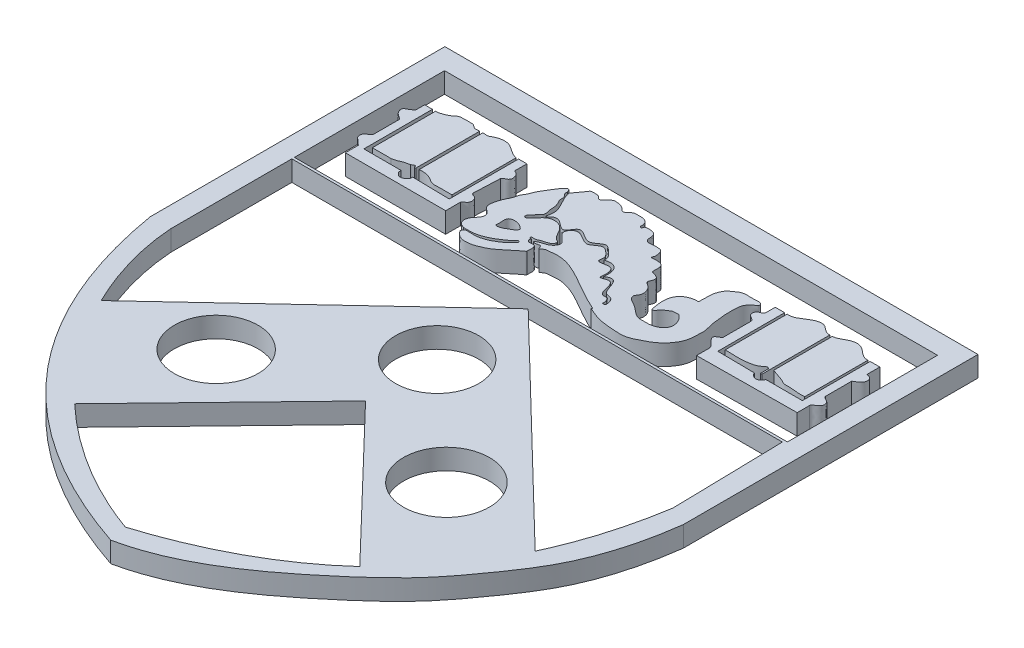
SolidWorks part; units mm, degrees
ref_plane "Front Plane" through (0, 0, 0) normal (0, 0, 1) x (1, 0, 0)
ref_plane "Top Plane" through (0, 0, 0) normal (0, 1, 0) x (1, 0, 0)
ref_plane "Right Plane" through (0, 0, 0) normal (1, 0, 0) x (0, 0, -1)
sketch "Sketch1" plane through (0, 0, 0) normal (0, 1, 0) x (1, 0, 0)
  line L0 (1055.163, 2168.8865) -> (3721.8297, 2168.8865) construction
  line L1 (1053.545, 3653.5487) -> (1053.545, 3267.9613)
  line L2 (1297.9682, 3681.7333) -> (1297.9682, 3287.744)
  line L3 (1316.3208, 3681.7333) -> (1316.3208, 3287.744)
  line L4 (1554.0703, 3653.5487) -> (1554.0703, 3254.3888)
  line L5 (1568.2519, 3653.5487) -> (1568.2519, 3223.5903)
  line L6 (1568.2519, 3653.5487) -> (1619.9728, 3653.5487)
  line L7 (1619.9728, 3653.5487) -> (1619.9728, 3576.7685)
  line L8 (1568.2519, 3223.5903) -> (1336.3345, 3227.698)
  line L9 (1053.545, 3227.698) -> (1265.4341, 3227.698)
  line L10 (985.1399, 3653.5487) -> (985.1399, 3605.7095)
  line L11 (985.1399, 3653.5487) -> (1033.524, 3653.5487)
  line L12 (1033.524, 3653.5487) -> (1033.524, 3227.698)
  line L13 (1053.545, 3227.698) -> (1033.524, 3227.698)
  line L14 (985.1399, 3498.0427) -> (985.1399, 3339.556)
  line L15 (996.8188, 3230.4747) -> (996.8188, 3149.381)
  line L16 (996.8188, 3149.381) -> (1619.9728, 3149.381)
  line L17 (1619.9728, 3149.381) -> (1619.9728, 3239.9995)
  line L18 (1617.5588, 3493.482) -> (1610.3296, 3327.7616)
  line L19 (1170.8678, 3260.4104) -> (1053.545, 3260.4104)
  line L20 (1053.545, 3267.9613) -> (1053.545, 3260.4104)
  line L21 (1336.3345, 3227.698) -> (1336.3345, 3211.9371)
  line L22 (3177.8193, 3149.381) -> (3797.5857, 3154.8466)
  line L23 (3797.5857, 3154.8466) -> (3797.5857, 3230.4747)
  line L24 (3177.8193, 3149.381) -> (3177.8193, 3230.4747)
  line L25 (3162.7219, 3329.8858) -> (3162.7219, 3504.8772)
  line L26 (3162.7219, 3597.4328) -> (3162.7219, 3653.5487)
  line L27 (3162.7219, 3653.5487) -> (3221.009, 3653.5487)
  line L28 (3221.009, 3653.5487) -> (3221.009, 3238.4503)
  line L29 (3221.009, 3238.4503) -> (3450.8371, 3235.5344)
  line L30 (3521.2215, 3235.5344) -> (3748.9975, 3235.5344)
  line L31 (3748.9975, 3235.5344) -> (3748.9975, 3656.8404)
  line L32 (3748.9975, 3656.8404) -> (3808.7099, 3656.8404)
  line L33 (3808.7099, 3656.8404) -> (3808.7099, 3575.71)
  line L34 (3797.5857, 3493.482) -> (3797.5857, 3329.8858)
  line L35 (3735.1617, 3656.8404) -> (3735.1617, 3263.852)
  line L36 (3496.718, 3674.201) -> (3496.718, 3310.4825)
  line L37 (3481.3079, 3674.201) -> (3481.3079, 3310.4825)
  line L38 (3236.4309, 3653.5487) -> (3236.4309, 3269.1002)
  line L39 (3481.3079, 3310.4825) -> (3481.3079, 3252.0377)
  line L40 (2620.7309, 3137.9842) -> (2603.084, 3137.9842)
  line L41 (2603.084, 3080.267) -> (2597.5849, 3074.3579)
  line L42 (863.2485, 2950.728) -> (3909.8084, 2950.728)
  line L43 (3909.8084, 2950.728) -> (3924.8369, 2257.8483)
  line L44 (863.2485, 2950.728) -> (863.2485, 2199.2152)
  line L45 (735.0259, 4029.3005) -> (4045.9931, 4029.3005)
  line L46 (4045.9931, 4029.3005) -> (4045.9931, 2199.2152)
  line L47 (735.0259, 4029.3005) -> (735.0259, 2199.2152)
  line L48 (1033.524, 1596.3018) -> (2404.1145, 2877.6897)
  line L49 (2404.1145, 2877.6897) -> (3728.7376, 1596.3018)
  line L50 (1506.2419, 958.9123) -> (2394.2693, 1877.4543)
  line L51 (2394.2693, 1877.4543) -> (3267.1424, 968.7322)
  line L53 (863.2485, 2966.6571) -> (3924.8369, 2966.6571)
  line L54 (863.2485, 2966.6571) -> (863.2485, 3899.0019)
  line L55 (863.2485, 3899.0019) -> (3924.8369, 3899.0019)
  line L56 (3924.8369, 2966.6571) -> (3924.8369, 3899.0019)
  circle A0 centre (2394.2693, 2322.3568) radius 258.1431
  circle A1 centre (3083.0456, 1690.9356) radius 267.0782
  circle A3 centre (1653.2592, 1690.9356) radius 260.2238
  spline S0 degree 3 poles (1766.7173, 3117.034) (1766.7029, 3095.9645) (1779.0838, 3074.514) (1799.0781, 3056.0781) (1831.6637, 3042.3492) (1860.0939, 3044.8782) (1890.0392, 3050.2679) (1911.6507, 3058.6086) (1984.0099, 3087.2819) (2032.2908, 3142.4193) (2093.3021, 3183.5003) (2092.8123, 3207.4894) (2133.5163, 3248.6941) (2195.3208, 3243.745) (2270.2529, 3243.0609) (2317.9495, 3217.8683) (2386.6086, 3184.733) (2454.854, 3147.5351) (2529.9518, 3105.2422) (2588.8084, 3078.0308) (2640.0464, 3055.8733) (2696.0271, 3036.6729) (2772.6708, 3029.9966) (2847.1621, 3023.3085) (2900.9777, 3046.7867) (2929.2486, 3062.4803) (2968.7548, 3081.1233) (3026.6254, 3124.3564) (3068.678, 3196.7845) (3068.9948, 3264.8359) (3074.3556, 3310.5622) (3058.1755, 3353.8007) (3053.6427, 3393.4851) (3049.5362, 3426.1512) (3047.1767, 3452.8144) (3045.4221, 3477.2709) (3046.2494, 3498.9535) (3047.0659, 3526.0773) (3047.6959, 3554.6198) (3064.3885, 3580.7259) (3082.5734, 3599.5304) (3104.4982, 3606.2292) (3103.0979, 3626.4649) (3080.6592, 3635.769) (3054.6615, 3629.2913) (3019.45, 3631.2515) (2991.2758, 3631.903) (2964.714, 3620.6343) (2946.8827, 3605.9478) (2922.3001, 3590.9718) (2908.9207, 3565.9652) (2898.4266, 3539.2885) (2896.7197, 3514.9553) (2896.1638, 3485.3948) (2893.6291, 3466.229) (2896.7461, 3442.5966) (2881.9665, 3445.8556) (2867.9132, 3444.0315) (2847.5459, 3439.2664) (2825.5248, 3429.8436) (2801.4388, 3411.4743) (2782.6127, 3377.028) (2777.901, 3327.6571) (2784.538, 3294.5569) (2790.5369, 3247.567) (2812.9215, 3270.2684) (2822.9924, 3284.9151) (2839.1427, 3297.4828) (2851.6326, 3304.5684) (2864.4182, 3313.8025) (2881.0712, 3313.7239) (2903.3143, 3317.4807) (2918.6086, 3301.3865) (2940.3869, 3274.1927) (2954.3391, 3219.5513) (2894.9992, 3167.9766) (2837.8281, 3169.1407) (2784.6996, 3170.6335) (2748.915, 3198.2923) (2710.9381, 3231.6848) (2665.0048, 3248.5809) (2659.4372, 3278.337) (2669.4671, 3289.6036) (2678.4382, 3306.9478) (2679.9936, 3331.8937) (2667.4607, 3359.2887) (2649.3862, 3376.9018) (2630.6806, 3386.3918) (2628.1023, 3401.758) (2637.963, 3416.0838) (2641.079, 3441.4737) (2620.6309, 3453.0252) (2606.8043, 3458.7933) (2589.9974, 3459.3239) (2587.8514, 3484.7524) (2592.3709, 3505.3837) (2582.1519, 3526.4327) (2565.9626, 3535.8598) (2544.5349, 3536.7131) (2528.0272, 3538.3391) (2505.8137, 3533.9211) (2518.1884, 3557.1564) (2512.6347, 3572.6521) (2511.3256, 3592.8879) (2498.5758, 3607.6521) (2474.6786, 3609.7059) (2447.4325, 3610.5776) (2418.1285, 3603.6687) (2398.9728, 3622.4994) (2401.732, 3645.4067) (2393.3513, 3673.9797) (2365.337, 3682.3876) (2344.1584, 3682.7948) (2321.9731, 3679.9622) (2323.808, 3662.3524) (2310.9214, 3664.7707) (2308.2288, 3673.9518) (2309.6864, 3683.9727) (2306.4934, 3697.3069) (2298.5989, 3711.994) (2283.2452, 3719.1331) (2266.9698, 3723.7251) (2248.5857, 3721.9195) (2230.8533, 3722.9875) (2215.0812, 3721.4175) (2204.317, 3713.3487) (2194.3558, 3706.4626) (2185.9559, 3694.7057) (2167.5848, 3693.5774) (2156.7164, 3708.5153) (2142.5117, 3718.494) (2125.3207, 3725.671) (2106.7925, 3725.4335) (2089.0621, 3729.1586) (2075.6789, 3718.31) (2059.7725, 3707.8587) (2050.6365, 3687.5589) (2029.1403, 3685.3413) (2022.0926, 3699.7624) (2007.0244, 3706.5133) (1990.5441, 3706.0884) (1976.751, 3706.8814) (1965.0026, 3705.0083) (1957.2056, 3694.6395) (1949.1528, 3680.8779) (1932.7806, 3661.8969) (1921.6046, 3643.8071) (1911.201, 3629.2241) (1896.8823, 3622.8361) (1894.3701, 3638.181) (1885.0151, 3652.4962) (1868.3146, 3636.8216) (1846.733, 3614.6048) (1826.5832, 3570.4032) (1796.8102, 3532.6688) (1788.312, 3499.3133) (1777.06, 3480.4456) (1761.4192, 3456.3989) (1759.2594, 3427.9924) (1741.8869, 3398.412) (1732.8837, 3375.1508) (1724.5478, 3345.0893) (1719.9666, 3321.9905) (1724.5312, 3300.0536) (1733.455, 3286.3738) (1747.6479, 3278.7142) (1759.285, 3268.9695) (1767.012, 3255.8689) (1768.7537, 3239.507) (1761.2534, 3221.2899) (1745.665, 3203.7775) (1728.3186, 3180.9618) (1722.9966, 3149.877) (1736.4375, 3127.6671) (1751.3612, 3119.3442) (1766.7173, 3117.034) (1766.7029, 3095.9645) (1779.0838, 3074.514) knots -0.007838 -0.005251 -0.002522 0 0.005656 0.01239 0.015798 0.026635 0.028667 0.034077 0.040466 0.075055 0.078282 0.0819 0.088117 0.110151 0.115482 0.133175 0.141137 0.161479 0.179658 0.192851 0.200326 0.213178 0.22804 0.246584 0.256741 0.262629 0.266031 0.282912 0.305526 0.312435 0.323659 0.33259 0.33962 0.347581 0.352344 0.355673 0.362282 0.365319 0.372006 0.379022 0.383081 0.388019 0.390336 0.393192 0.400959 0.406206 0.414341 0.417445 0.423284 0.428179 0.434405 0.439757 0.445317 0.448956 0.457208 0.458539 0.460712 0.463584 0.468046 0.472776 0.478007 0.485839 0.495787 0.505719 0.510762 0.51486 0.519077 0.522758 0.526657 0.527821 0.532088 0.536287 0.540515 0.544209 0.557818 0.568272 0.586122 0.590945 0.599687 0.611761 0.622578 0.625392 0.628081 0.631119 0.637125 0.642229 0.64866 0.652412 0.653529 0.65754 0.662536 0.666454 0.670152 0.671995 0.67544 0.682234 0.685631 0.68846 0.693111 0.697808 0.700006 0.703062 0.708061 0.710804 0.714913 0.718382 0.724678 0.731928 0.734149 0.739639 0.744834 0.75059 0.755018 0.758916 0.760857 0.762735 0.764141 0.766243 0.768768 0.772249 0.7758 0.778528 0.782352 0.786682 0.789308 0.791554 0.794592 0.796579 0.799964 0.803594 0.807013 0.810397 0.814482 0.818258 0.820352 0.824402 0.82974 0.832473 0.835088 0.838359 0.841821 0.844874 0.846783 0.848544 0.852307 0.856483 0.863521 0.864775 0.867645 0.869872 0.872557 0.875941 0.880286 0.892777 0.903622 0.908934 0.9131 0.91676 0.926013 0.92936 0.937236 0.94087 0.948142 0.95099 0.954138 0.957552 0.960532 0.963143 0.966489 0.969986 0.974608 0.980518 0.987045 0.992162 0.994749 0.997478 1 1.005656 1.01239 1.015798 only from (1767.354, 3102.4011) to (1767.354, 3102.4011)
  spline S1 degree 3 poles (1764.3416, 3114.6521) (1774.7587, 3114.5124) (1790.7318, 3114.8796) (1812.9946, 3114.2797) (1833.9847, 3116.5519) (1859.1341, 3122.3504) (1888.4662, 3132.584) (1919.294, 3148.3083) (1949.8195, 3167.4242) (1976.3209, 3185.9161) (1992.5983, 3200.3327) (1998.8827, 3211.3406) (2005.2863, 3213.0932) (2011.9248, 3214.9603) (2015.454, 3208.0898) (2015.4918, 3200.9802) (2009.0505, 3194.8054) (2002.5129, 3188.21) (1985.159, 3172.0218) (1964.945, 3153.3955) (1937.1117, 3137.8578) (1915.46, 3124.8962) (1891.3271, 3116.7862) (1866.5389, 3108.381) (1833.9275, 3106.6758) (1807.6578, 3106.7885) (1782.19, 3108.7411) (1776.6957, 3097.3707) (1771.1382, 3088.8932) (1773.9955, 3084.3982) knots 0 0 0 0 0.054417 0.083521 0.116256 0.164417 0.218115 0.278186 0.344753 0.406485 0.446167 0.459403 0.468414 0.481036 0.488834 0.504337 0.514961 0.533717 0.553539 0.638662 0.676228 0.719841 0.770141 0.808715 0.856477 0.936886 0.958327 0.972461 1 1 1 1
  spline S2 degree 3 poles (1853.4295, 3248.3638) (1848.7837, 3220.1528) (1884.8545, 3229.1277) (1904.9358, 3240.4346) (1925.5238, 3252.7771) (1942.5187, 3262.8179) (1953.61, 3279.8222) (1940.6636, 3291.371) (1928.0464, 3300.3614) (1908.1616, 3308.8236) (1885.3497, 3311.8724) (1858.8561, 3307.5294) (1850.6984, 3285.9089) (1852.7034, 3266.1845) (1853.4295, 3248.3638) (1848.7837, 3220.1528) (1884.8545, 3229.1277) knots -0.196313 -0.1285 -0.045091 0 0.118995 0.183982 0.265854 0.354672 0.401688 0.433407 0.51208 0.570069 0.649855 0.754912 0.803687 0.8715 0.954909 1 1.118995 1.183982 1.265854 only from (1852.3547, 3230.4747) to (1852.3547, 3230.4747)
  spline S3 degree 3 poles (1898.5546, 3627.0014) (1889.3806, 3608.1039) (1917.5972, 3598.0372) (1916.0916, 3574.9578) (1915.2917, 3563.2224) (1921.4576, 3548.5585) (1934.5002, 3527.4126) (1938.8511, 3504.5861) (1937.8034, 3484.6448) (1940.7565, 3473.0301) (1945.7639, 3458.7699) (1944.4878, 3445.25) (1944.5568, 3433.9138) (1938.4282, 3428.7399) (1931.7831, 3423.4754) (1924.006, 3414.2369) (1917.4588, 3400.0889) (1904.6299, 3390.0601) (1895.1302, 3379.3494) (1892.2196, 3362.0819) (1909.2131, 3359.5058) (1918.6245, 3369.3348) (1931.6369, 3380.139) (1944.1482, 3396.4872) (1960.1505, 3415.0068) (1980.6215, 3431.1044) (2009.7917, 3435.8071) (2039.6926, 3432.1353) (2070.4362, 3411.3252) (2091.102, 3376.0895) (2108.1112, 3342.1268) (2138.7004, 3329.8121) (2134.9914, 3311.0758) (2122.4927, 3298.3896) (2102.6878, 3291.0037) (2072.54, 3285.7335) (2053.3185, 3268.7134) (2024.6663, 3278.4843) (2027.7707, 3260.8257) (2040.9852, 3266.2472) (2030.6837, 3251.532) (2045.0721, 3234.7338) (2064.7965, 3241.6285) (2086.7479, 3238.3075) (2092.8446, 3212.2892) (2089.2049, 3196.4857) (2090.4298, 3184.3996) knots 0 0 0 0 0.055655 0.063679 0.077752 0.095904 0.116878 0.163693 0.172304 0.185424 0.204638 0.223398 0.23251 0.241509 0.249141 0.262153 0.282474 0.302047 0.31658 0.333553 0.347506 0.361341 0.378962 0.406094 0.431577 0.463686 0.492892 0.530956 0.564788 0.616478 0.669611 0.694524 0.71222 0.723965 0.755621 0.782578 0.827891 0.84317 0.854771 0.863118 0.871847 0.893466 0.919754 0.939988 0.960257 1 1 1 1
  spline S4 degree 3 poles (1619.9728, 3576.7685) (1628.9817, 3574.4235) (1643.5368, 3567.2409) (1652.3448, 3546.6177) (1656.7088, 3527.33) (1645.1007, 3510.4233) (1629.2003, 3505.1898) (1621.8598, 3497.4992) (1617.5588, 3493.482) knots 0 0 0 0 0.253373 0.370433 0.57552 0.732955 0.846761 1 1 1 1
  spline S5 degree 3 poles (1610.3296, 3327.7616) (1614.4439, 3317.8178) (1630.1093, 3318.1005) (1650.6294, 3300.0497) (1653.3259, 3262.0541) (1626.3274, 3250.9211) (1619.9728, 3239.9995) knots 0 0 0 0 0.213854 0.368491 0.668361 1 1 1 1
  spline S6 degree 3 poles (996.8188, 3230.4747) (984.4458, 3239.2517) (970.904, 3255.2197) (945.3409, 3274.1852) (945.0101, 3303.1226) (967.8836, 3319.5433) (983.6248, 3327.8596) (985.1399, 3339.556) knots 0 0 0 0 0.311087 0.438097 0.641301 0.787744 1 1 1 1
  spline S7 degree 3 poles (985.1399, 3498.0427) (971.8487, 3511.0885) (942.5391, 3519.7426) (930.7245, 3567.1075) (958.1348, 3577.2644) (974.1961, 3589.2706) (987.0865, 3597.7672) (985.1399, 3605.7095) knots 0 0 0 0 0.365771 0.573476 0.74555 0.855625 1 1 1 1
  spline S8 degree 3 poles (1316.3208, 3287.744) (1340.3222, 3291.6682) (1373.3639, 3287.3159) (1409.0161, 3266.2797) (1435.4158, 3249.7319) (1487.5848, 3258.1016) (1526.2796, 3251.929) (1554.0703, 3254.3888) knots 0 0 0 0 0.299471 0.382757 0.509916 0.665981 1 1 1 1
  spline S9 degree 3 poles (1297.9682, 3287.744) (1291.6979, 3282.075) (1285.2182, 3287.5648) (1287.4313, 3294.9438) (1283.8742, 3297.5735) (1279.57, 3296.8141) (1274.1473, 3295.7109) (1269.7751, 3289.8867) (1263.7912, 3290.3806) (1262.0171, 3287.744) knots 0 0 0 0 0.311089 0.387238 0.451371 0.558854 0.66626 0.807713 1 1 1 1
  spline S10 degree 3 poles (1262.0171, 3287.744) (1256.1642, 3285.8833) (1245.9104, 3282.3315) (1232.4467, 3281.9809) (1222.4946, 3276.9397) (1211.9015, 3273.5699) (1199.1841, 3266.7888) (1184.3345, 3265.3823) (1175.5246, 3259.6143) (1170.8678, 3260.4104) knots 0 0 0 0 0.192896 0.339053 0.412268 0.539463 0.688167 0.858735 1 1 1 1
  spline S11 degree 3 poles (1053.545, 3653.5487) (1063.893, 3652.0907) (1081.0696, 3656.0843) (1105.3454, 3665.674) (1125.1631, 3675.0677) (1140.8151, 3687.9234) (1154.2824, 3698.8268) (1172.1209, 3699.9442) (1199.3312, 3700.9189) (1221.6862, 3699.7928) (1237.6016, 3699.8033) knots 0 0 0 0 0.157367 0.266054 0.401879 0.489817 0.578729 0.658567 0.755752 1 1 1 1
  spline S12 degree 3 poles (1237.6016, 3699.8033) (1245.5565, 3698.2497) (1254.286, 3689.3112) (1273.7883, 3677.6683) (1289.0367, 3684.0898) (1297.9682, 3681.7333) knots 0 0 0 0 0.356877 0.568619 1 1 1 1
  spline S13 degree 1 poles (1265.4341, 3227.698) (1265.4341, 3211.0876) knots 0 0 1 1
  spline S14 degree 3 poles (1265.4341, 3211.0876) (1267.6342, 3208.3659) (1271.9534, 3205.1227) (1276.9643, 3199.1352) (1281.6177, 3194.9842) (1293.8421, 3184.8347) (1320.1869, 3191.6075) (1331.0668, 3206.429) (1336.3345, 3211.9371) knots 0 0 0 0 0.121795 0.187143 0.272069 0.34032 0.735442 1 1 1 1
  spline S15 degree 3 poles (1316.3208, 3681.7333) (1324.4815, 3685.6847) (1344.2103, 3676.886) (1364.9222, 3690.3679) (1384.2267, 3700.3962) (1411.4612, 3707.7506) (1476.6456, 3710.9985) (1514.3803, 3657.9053) (1554.0703, 3653.5487) knots 0 0 0 0 0.103997 0.214763 0.270843 0.362032 0.545668 1 1 1 1
  spline S16 degree 3 poles (3236.4309, 3269.1002) (3285.8713, 3268.3332) (3361.8953, 3260.5303) (3437.7984, 3288.1424) (3461.2791, 3314.4448) (3472.1125, 3300.8226) knots 0 0 0 0 0.63664 0.861829 1 1 1 1
  spline S17 degree 1 poles (3472.1125, 3300.8226) (3472.2974, 3252.1679) knots 0 0 1 1
  spline S18 degree 2 poles (3472.2974, 3252.1679) (3476.8066, 3248.7155) (3481.3079, 3252.0377) knots 0 0 0 1 1 1
  spline S19 degree 2 poles (3450.8371, 3235.5344) (3458.5336, 3211.3882) (3490.4759, 3207.658) knots 0 0 0 1 1 1
  spline S20 degree 3 poles (3490.4759, 3207.658) (3504.664, 3208.7812) (3520.008, 3220.7748) (3521.2215, 3235.5344) knots 0 0 0 0 1 1 1 1
  spline S21 degree 3 poles (3797.5857, 3230.4747) (3798.0757, 3242.6653) (3829.7413, 3253.3982) (3848.252, 3281.6101) (3831.6101, 3304.5952) knots 0 0 0 0 0.341602 1 1 1 1
  spline S22 degree 3 poles (3797.5857, 3329.8858) (3798.5687, 3325.5044) (3809.6745, 3315.7982) (3823.428, 3310.9714) (3831.6101, 3304.5952) knots 0 0 0 0 0.287594 1 1 1 1
  spline S23 degree 3 poles (3797.5857, 3493.482) (3807.3891, 3500.8623) (3827.5981, 3508.0628) (3843.9522, 3530.7047) (3846.5902, 3551.8829) (3833.8558, 3570.9761) (3818.1814, 3575.7693) (3808.7099, 3575.71) knots 0 0 0 0 0.294297 0.490042 0.636412 0.773294 1 1 1 1
  spline S24 degree 3 poles (3496.718, 3674.201) (3527.689, 3675.4143) (3563.8986, 3710.979) (3630.1101, 3717.3288) (3677.6666, 3683.0208) (3705.4485, 3654.3844) (3735.1617, 3656.8404) knots 0 0 0 0 0.343693 0.549958 0.698809 1 1 1 1
  spline S25 degree 3 poles (3481.3079, 3674.201) (3450.2013, 3669.6656) (3426.8879, 3714.6601) (3332.3554, 3709.9183) (3290.7959, 3646.39) (3236.4309, 3653.5487) knots 0 0 0 0 0.316549 0.427998 1 1 1 1
  spline S26 degree 3 poles (3496.718, 3310.4825) (3524.6115, 3297.4133) (3562.8675, 3291.1201) (3600.8955, 3266.9358) (3653.4025, 3271.4058) (3694.153, 3258.8578) (3735.1617, 3263.852) knots 0 0 0 0 0.372329 0.471818 0.523942 1 1 1 1
  spline S27 degree 3 poles (3177.8193, 3230.4747) (3171.0674, 3254.2081) (3146.6633, 3264.3944) (3118.2165, 3310.0874) (3160.0283, 3320.2307) (3162.7219, 3329.8858) knots 0 0 0 0 0.493606 0.660952 1 1 1 1
  spline S28 degree 3 poles (3162.7219, 3504.8772) (3156.7147, 3522.144) (3118.1229, 3525.2154) (3124.5678, 3582.5318) (3160.7152, 3576.9015) (3162.7219, 3597.4328) knots 0 0 0 0 0.405154 0.64783 1 1 1 1
  spline S29 degree 2 poles (1929.9633, 3569.6444) (2365.2867, 3792.7012) (2649.717, 3269.1002) knots 0 0 0 1 1 1
  spline S30 degree 1 poles (2649.717, 3269.1002) (2663.1136, 3263.852) knots 0 0 1 1
  spline S31 degree 3 poles (1908.0502, 3628.5045) (1917.4315, 3561.6357) (1988.3399, 3512.9533) (1959.4286, 3434.3671) knots 0 0 0 0 1 1 1 1
  spline S32 degree 3 poles (1959.4286, 3434.3671) (1967.2599, 3426.6729) (1980.2612, 3448.8799) (2030.5976, 3463.628) (2090.43, 3373.6741) (2135.5124, 3508.3766) (2228.7008, 3384.524) (2294.546, 3482.6563) (2350.9328, 3429.5317) (2382.354, 3404.9512) (2376.7283, 3376.2609) knots 0 0 0 0 0.046897 0.113659 0.283898 0.409479 0.615731 0.768766 0.854489 1 1 1 1
  spline S33 degree 2 poles (2376.7283, 3376.2609) (2476.1154, 3403.7327) (2464.767, 3284.8705) knots 0 0 0 1 1 1
  spline S34 degree 3 poles (2464.767, 3284.8705) (2543.2698, 3341.7683) (2526.9192, 3193.474) (2612.6947, 3199.9831) (2625.6074, 3156.6547) (2620.7309, 3137.9842) knots 0 0 0 0 0.586831 0.719708 1 1 1 1
  spline S35 degree 3 poles (2603.084, 3137.9842) (2609.6129, 3150.7229) (2597.7116, 3187.9086) (2568.5465, 3179.847) (2547.3809, 3190.7702) (2535.677, 3228.9997) (2522.4596, 3303.4542) (2448.4972, 3255.3954) (2463.3064, 3315.3899) (2444.9095, 3379.1383) (2350.1913, 3331.9812) (2371.2084, 3394.7343) (2346.7662, 3416.9992) (2328.0062, 3435.7284) (2287.0896, 3452.3886) (2251.6969, 3397.5162) (2191.6779, 3424.7643) (2139.6778, 3466.6296) (2071.9188, 3382.5811) (2180.6491, 3344.7236) (2124.9487, 3275.8948) (2090.9319, 3278.6786) (2052.3192, 3255.1121) (2082.4961, 3248.3825) (2106.9816, 3265.5394) (2111.7936, 3226.4441) (2132.1686, 3250.4821) (2160.8907, 3252.5251) (2234.2424, 3263.7352) (2331.3122, 3228.1647) (2457.4767, 3154.5254) (2543.9021, 3105.8115) (2603.084, 3080.267) knots 0 0 0 0 0.032556 0.042949 0.052817 0.07463 0.120722 0.149452 0.169594 0.207059 0.251665 0.273961 0.296134 0.310451 0.325904 0.373059 0.395061 0.44379 0.478197 0.537519 0.563826 0.609543 0.61687 0.626604 0.647837 0.659656 0.672274 0.686951 0.717995 0.810907 0.876411 1 1 1 1
  spline S36 degree 2 poles (735.0259, 2199.2152) (970.8433, 803.8457) (2351.3646, 337.5663) knots 0 0 0 1 1 1
  spline S37 degree 3 poles (4045.9931, 2199.2152) (4019.036, 1992.1579) (3940.6058, 1686.04) (3715.6274, 1353.3783) (3523.9158, 1090.6855) (3098.5224, 703.7526) (2693.6842, 409.0142) (2351.3646, 337.5663) knots 0 0 0 0 0.238562 0.347751 0.454 0.606191 1 1 1 1
  spline S38 degree 3 poles (863.2485, 2199.2152) (877.4731, 1989.4031) (1118.7753, 1216.1279) (1775.9472, 650.7534) (2327.2408, 452.8291) knots 0 0 0 0 0.263514 1 1 1 1
  spline S39 degree 2 poles (3924.8369, 2257.8483) (3711.1137, 888.5928) (2327.2408, 452.8291) knots 0 0 0 1 1 1
extrude "Boss-Extrude2" add sketch "Sketch1" along normal blind 127 contours L0 L48 S38 L50 L51 S39 L49 A0 A3 A1 | L48 L0 A0 L49 | S37 L46 L45 L47 S36 L56 L53 L54 L55 L43 S39 S38 L44 L42 | L40 S35 L41 S0 S30 S29 S31 S32 S33 S34 | S0 S31 S29 S30 | S3 S0 S1 S2 | S28 L25 S27 L24 L22 L23 S21 S22 L34 S23 L33 L32 L31 L30 S20 S19 L29 L28 L27 L26 | L37 S25 L38 S16 S17 S18 L39 | L36 S26 L35 S24 | S12 S11 L1 L20 L19 S10 S9 L2 | S15 L3 S8 L4 | S14 S13 L9 L13 L12 L11 L10 S7 L14 S6 L15 L16 L17 S5 L18 S4 L7 L6 L5 L8 L21
